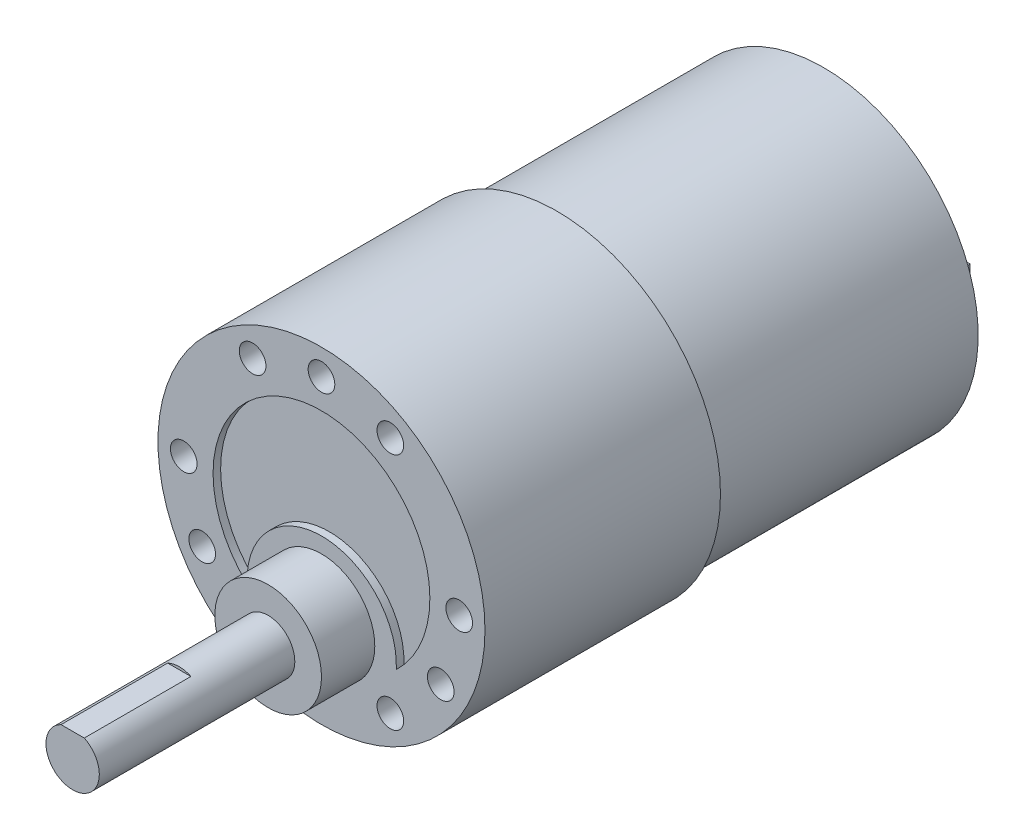
SolidWorks part; units mm, degrees
ref_plane "Alzado" through (0, 0, 0) normal (0, 0, 1) x (1, 0, 0)
ref_plane "Planta" through (0, 0, 0) normal (0, 1, 0) x (1, 0, 0)
ref_plane "Vista lateral" through (0, 0, 0) normal (1, 0, 0) x (0, 0, -1)
sketch "Croquis1" plane through (0, 0, 0) normal (0, 0, 1) x (1, 0, 0)
  circle A0 centre (0, 0) radius 18.4
  dimension "D1" = 36.8
extrude "Saliente-Extruir1" add sketch "Croquis1" along normal blind 26.5
sketch "Croquis2" plane through (0, 0, 26.5) normal (0, 0, 1) x (1, 0, 0)
  line L0 (0, 30.4942) -> (0, -33.5704) construction
  arc A0 (8.419, -8.8295) -> (-8.3557, -8.8894) centre (0, 0) ccw
  circle A1 centre (0, 0) radius 18.4
  circle A2 centre (0, 0) radius 18.4
  circle A4 centre (0, 0) radius 12.2 construction
  arc A6 (-8.3557, -8.8894) -> (8.419, -8.8295) centre (0.03, -8.3999) cw
  dimension "D5" = 8.4
  dimension "D6" = 16.7747
  dimension "D1" = 0
  dimension "D2" = 6.2
extrude "Cortar-Extruir2" cut sketch "Croquis2" against normal blind 0.85
sketch "Croquis3" plane through (0, 0, 26.5) normal (0, 0, 1) x (1, 0, 0)
  line L0 (0, 31.1583) -> (0, -27.634) construction
  line L1 (0, 0) -> (0, 15.5) construction
  line L2 (0, 0) -> (13.4234, -7.75) construction
  circle A0 centre (0, 15.5) radius 1.5
  circle A1 centre (13.4234, -7.75) radius 1.5
  circle A2 centre (-13.4234, -7.75) radius 1.5
  dimension "D1" = 3
  dimension "D2" = 15.5
  dimension "D4" = 120
  dimension "D5" = 15.5
  dimension "D6" = 120
  dimension "D3" = 3
extrude "Cortar-Extruir3" cut sketch "Croquis3" against normal blind 25
sketch "Croquis9" plane through (0, 0, 26.5) normal (0, 0, 1) x (1, 0, 0)
  line L0 (0, 24.3626) -> (0, -23.3935) construction
  line L1 (-26.4176, 0) -> (25.549, 0) construction
  line L2 (0, 0) -> (-15.5, 0) construction
  circle A0 centre (-15.5, 0) radius 1.5
  circle A1 centre (-7.75, 13.4234) radius 1.5
  circle A2 centre (7.75, 13.4234) radius 1.5
  circle A3 centre (15.5, 0) radius 1.5
  circle A4 centre (7.75, -13.4234) radius 1.5
  circle A5 centre (-7.75, -13.4234) radius 1.5
  dimension "D1" = 3
  dimension "D2" = 15.5
  dimension "D4" = 15.5
  dimension "D3" = 6
extrude "Cortar-Extruir4" cut sketch "Croquis9" against normal blind 5
sketch "Croquis22" plane through (0, 0, 26.5) normal (0, 0, 1) x (1, 0, 0)
  line L0 (13.4234, -7.75) -> (-13.4234, -7.75) construction
  circle A0 centre (0, -7.75) radius 6
  circle A1 centre (0, 0) radius 18.4
  circle A2 centre (0, 0) radius 18.4
  dimension "D2" = 12
  dimension "D1" = 0
extrude "Saliente-Extruir2" add sketch "Croquis22" along normal blind 6 contours A0
sketch "Croquis24" plane through (0, 0, 32.5) normal (0, 0, 1) x (1, 0, 0)
  circle A0 centre (0, -7.75) radius 3
  dimension "D1" = 6
extrude "Saliente-Extruir3" add sketch "Croquis24" along normal blind 22
sketch "Croquis25" plane through (0, 0, 54.5) normal (0, 0, 1) x (1, 0, 0)
  line L0 (4.0248, -7.75) -> (-5.0416, -7.75) construction
  line L1 (0, -3.7978) -> (0, -11.5749) construction
  line L2 (-1.3077, -5.05) -> (1.3077, -5.05)
  circle A0 centre (0, -7.75) radius 3 construction
  circle A1 centre (0, -7.75) radius 3
  circle M4 centre (0, -7.75) radius 3
  dimension "D1" = 2.7
extrude "Cortar-Extruir5" cut sketch "Croquis25" against normal blind 12 contours L2 M4
sketch "Croquis26" plane through (0, 0, 0) normal (0, 0, -1) x (-1, 0, 0)
  circle A0 centre (0, 0) radius 17.4
  circle A1 centre (0, 0) radius 18.4
  circle A2 centre (0, 0) radius 18.4
  dimension "D1" = 0
  dimension "D2" = 1
extrude "Saliente-Extruir4" add sketch "Croquis26" along normal blind 30 contours A0
sketch "Croquis27" plane through (0, 0, -30) normal (0, 0, -1) x (-1, 0, 0)
  line L0 (-25.3398, 0) -> (26.5759, 0) construction
  line L1 (0, 15.9533) -> (0, -14.6399) construction
  line L2 (11.5, -1.5) -> (11, 1.5) construction
  line L3 (-11.5, -1.5) -> (-11, -1.5)
  line L4 (-11.5, -1.5) -> (-11.5, 1.5)
  line L5 (-11.5, 1.5) -> (-11, 1.5)
  line L6 (-11, -1.5) -> (-11, 1.5)
  line L7 (-11.5, -1.5) -> (-11, 1.5) construction
  line L8 (-11.5, 1.5) -> (-11, -1.5) construction
  line L9 (11.5, 1.5) -> (11, -1.5) construction
  line L10 (11.5, 1.5) -> (11, 1.5)
  line L11 (11, -1.5) -> (11, 1.5)
  line L12 (11.5, -1.5) -> (11, -1.5)
  line L13 (11.5, -1.5) -> (11.5, 1.5)
  circle A0 centre (0, 0) radius 3.9
  circle A1 centre (-11.25, 0) radius 2.25
  circle A2 centre (11.25, 0) radius 2.25
  dimension "D1" = 7.8
  dimension "D2" = 4.5
  dimension "D3" = 11.25
  dimension "D4" = 3
  dimension "D5" = 0.5
extrude "Saliente-Extruir5" add sketch "Croquis27" along normal blind 1.6
sketch "Croquis29" plane through (0, 0, -30) normal (0, 0, -1) x (-1, 0, 0)
  line L0 (-11, -1.5) -> (-11, 1.5) construction
  line L1 (-11, 1.5) -> (-11.5, 1.5) construction
  line L2 (-11.5, 1.5) -> (-11.5, -1.5) construction
  line L3 (-11.5, -1.5) -> (-11, -1.5) construction
  line L4 (11.5, -1.5) -> (11.5, 1.5) construction
  line L5 (11.5, 1.5) -> (11, 1.5) construction
  line L6 (11, 1.5) -> (11, -1.5) construction
  line L7 (11, -1.5) -> (11.5, -1.5) construction
  line L8 (-11, -1.5) -> (-11, 1.5)
  line L9 (-11, 1.5) -> (-11.5, 1.5)
  line L10 (-11.5, 1.5) -> (-11.5, -1.5)
  line L11 (-11.5, -1.5) -> (-11, -1.5)
  line L12 (11.5, -1.5) -> (11.5, 1.5)
  line L13 (11.5, 1.5) -> (11, 1.5)
  line L14 (11, 1.5) -> (11, -1.5)
  line L15 (11, -1.5) -> (11.5, -1.5)
extrude "Saliente-Extruir6" add sketch "Croquis29" along normal blind 5
